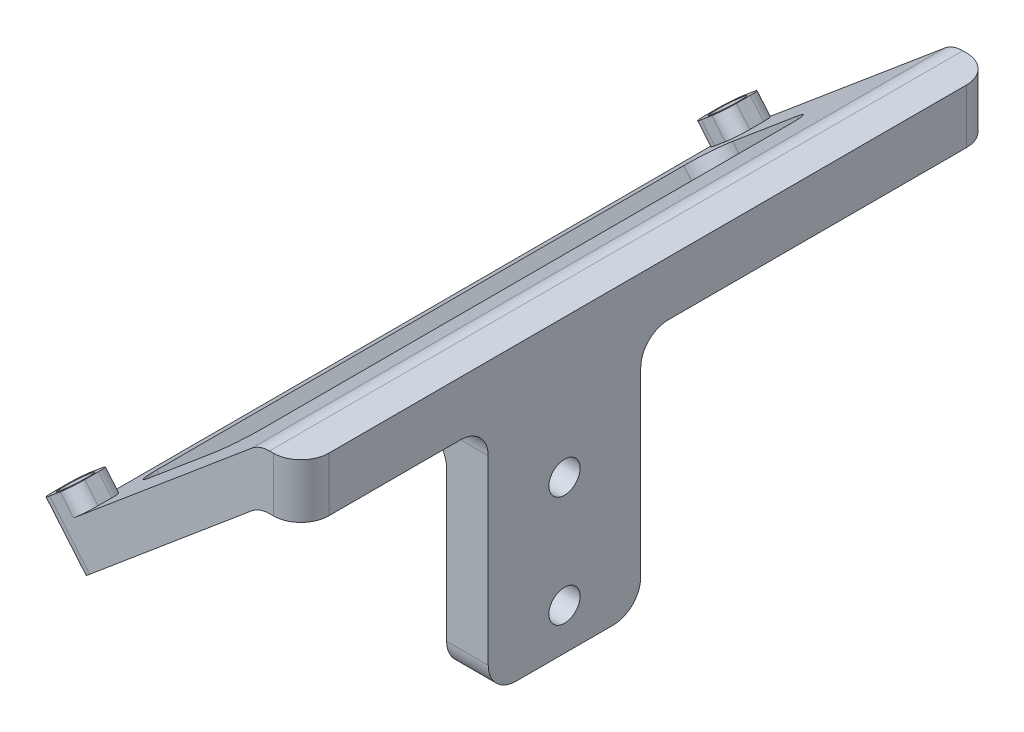
SolidWorks part; units mm, degrees
ref_plane "Front" through (0, 0, 0) normal (0, 0, 1) x (1, 0, 0)
ref_plane "Top" through (0, 0, 0) normal (0, 1, 0) x (1, 0, 0)
ref_plane "Right" through (0, 0, 0) normal (1, 0, 0) x (0, 0, -1)
sketch "Esquisse1" plane through (0, 0, 0) normal (0, 0, 1) x (1, 0, 0)
  line L0 (0, 0) -> (0, 34.1676)
  line L1 (0, 34.1676) -> (-26.019, 12.335)
  line L2 (-26.019, 12.335) -> (-29.8757, 16.9313)
  line L3 (-29.8757, 16.9313) -> (0, 42)
  line L4 (0, 42) -> (6, 42)
  line L5 (6, 42) -> (6, 0)
  line L6 (6, 0) -> (0, 0)
  line L7 (0, 34.1676) -> (0, 42) construction
  dimension "D1" = 6
  dimension "D2" = 6
  dimension "D3" = 50
  dimension "D4" = 42
  dimension "D5" = 39
extrude "Boss.-Extru.1" add sketch "Esquisse1" along normal blind 100
sketch "Esquisse2" plane through (-20.681, 24.6466, 0) normal (-0.6428, 0.766, 0) x (0.766, 0.6428, 0)
  line L0 (-12.0029, -50) -> (26.9971, -50) construction
  line L1 (-12.0029, -100) -> (-6.0029, -100)
  line L2 (-12.0029, -100) -> (-12.0029, -94)
  line L3 (-12.0029, -94) -> (-6.0029, -94)
  line L4 (-6.0029, -100) -> (-6.0029, -94)
  line L5 (-12.0029, -100) -> (-12.0029, 0) construction
  line L6 (26.9971, -100) -> (26.9971, 0) construction
  line L7 (-6.0029, 0) -> (-6.0029, -6)
  line L8 (-12.0029, -6) -> (-6.0029, -6)
  line L9 (-12.0029, 0) -> (-12.0029, -6)
  line L10 (-12.0029, 0) -> (-6.0029, 0)
  dimension "D1" = 6
  dimension "D2" = 6
extrude "Boss.-Extru.2" add sketch "Esquisse2" along normal blind 3
sketch "Esquisse3" plane through (-22.6093, 26.9447, 0) normal (-0.6428, 0.766, 0) x (0.766, 0.6428, 0)
  line L0 (-12.0029, -100) -> (-6.0029, -100) construction
  line L1 (-12.0029, -94) -> (-12.0029, -100) construction
  line L2 (-12.0029, -50) -> (26.9971, -50) construction
  line L3 (-12.0029, -94) -> (-12.0029, -6) construction
  line L4 (26.9971, -100) -> (26.9971, 0) construction
  circle A0 centre (-9.0029, -97) radius 2.25
  circle A1 centre (-9.0029, -3) radius 2.25
  point P4 (-9.0029, -100)
  dimension "D2" = 3
  dimension "D3" = 4.5
  dimension "D1" = 3
extrude "Enlèv. mat.-Extru.1" cut sketch "Esquisse3" against normal blind 5
sketch "Esquisse4" plane through (-19.3954, 23.1145, 0) normal (-0.6428, 0.766, 0) x (0.766, 0.6428, 0)
  circle A0 centre (-9.0029, -97) radius 1.75
  circle A1 centre (-9.0029, -3) radius 1.75
  dimension "D1" = 3.5
extrude "Enlèv. mat.-Extru.2" cut sketch "Esquisse4" against normal through all both and the other way through all
fillet "Congé1" radius 2 8 edges at (-28.9116, 15.7822, 0) (-26.2436, 21.9371, 0) (-26.2436, 21.9371, 6) (-30.8399, 18.0803, 6) (-30.8399, 18.0803, 94) (-26.2436, 21.9371, 94) (-26.2436, 21.9371, 100) (-28.9116, 15.7822, 100)
sketch "Esquisse5" plane through (6, 0, 0) normal (1, 0, 0) x (0, 0, -1)
  line L0 (-100, 34.1676) -> (0, 34.1676) construction
  line L1 (-100, 0) -> (-73, 0)
  line L2 (-100, 0) -> (-100, 34.1676)
  line L3 (-100, 34.1676) -> (-73, 34.1676)
  line L4 (-73, 0) -> (-73, 34.1676)
  line L6 (0, 0) -> (-51, 0)
  line L7 (0, 0) -> (0, 34.1676)
  line L8 (0, 34.1676) -> (-51, 34.1676)
  line L9 (-51, 0) -> (-51, 34.1676)
  dimension "D1" = 27
  dimension "D2" = 51
extrude "Enlèv. mat.-Extru.3" cut sketch "Esquisse5" against normal up to vertex (6 mm away) up to point (0, 34.1676, 100)
fillet "Congé2" radius 4 1 edges at (0, 34.1676, 62)
sketch "Esquisse6" plane through (-20.681, 24.6466, 0) normal (-0.6428, 0.766, 0) x (0.766, 0.6428, 0)
  line L0 (-12.0029, -96) -> (-12.0029, -4) construction
  line L1 (-8.0029, -8) -> (11.9971, -8)
  line L2 (-8.0029, -8) -> (-8.0029, -92)
  line L3 (-8.0029, -92) -> (11.9971, -92)
  line L4 (11.9971, -8) -> (11.9971, -92)
  line L8 (-8.0029, -50) -> (-12.0029, -50) construction
  line L9 (-8.0029, -94) -> (-10.0029, -94) construction
  point P11 (-9.0029, -94)
  dimension "D1" = 4
  dimension "D2" = 20
  dimension "D3" = 2
extrude "Enlèv. mat.-Extru.5" cut sketch "Esquisse6" against normal up to vertex (6 mm away) up to point (-24.4869, 13.6206, 0)
fillet "Congé3" radius 4 13 edges at (0, 34.1676, 86.5) (0, 34.1676, 25.5) (0, 42, 50) (6, 38.0838, 0) (6, 38.0838, 100) (3, 34.1676, 51) (3, 34.1676, 73) (-9.5623, 30.0601, 92) (-24.8832, 17.2043, 92) (-24.8832, 17.2043, 8) (-9.5623, 30.0601, 8) (3, 0, 51) (3, 0, 73)
sketch "Esquisse7" plane through (6, 0, 0) normal (1, 0, 0) x (0, 0, -1)
  line L0 (-62, 0) -> (-62, 22) construction
  line L1 (-69, 0) -> (-55, 0) construction
  circle A0 centre (-62, 22) radius 2.25
  circle A1 centre (-62, 6) radius 2.25
  dimension "D1" = 16
  dimension "D2" = 4.5
  dimension "D3" = 6
extrude "Enlèv. mat.-Extru.6" cut sketch "Esquisse7" against normal up to vertex (6 mm away)
